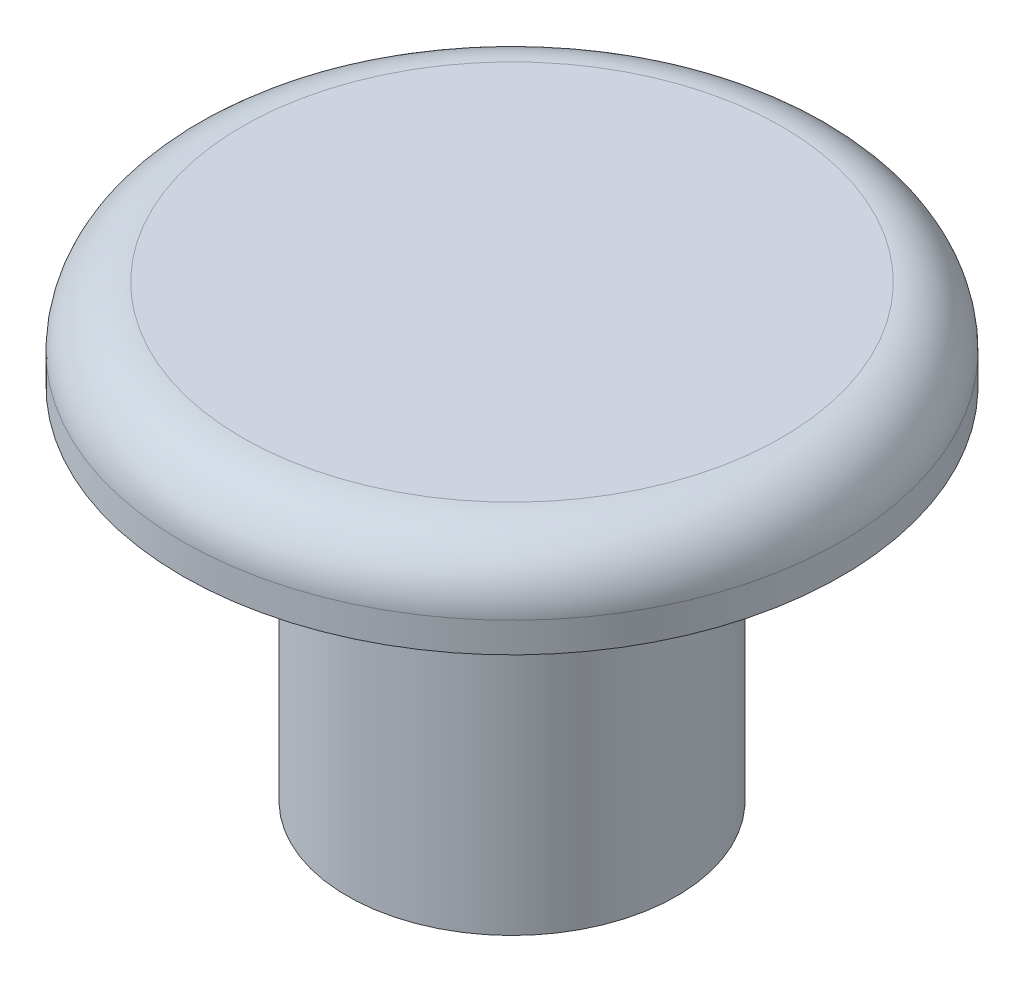
SolidWorks part; units mm, degrees
ref_plane "Front Plane" through (0, 0, 0) normal (0, 0, 1) x (1, 0, 0)
ref_plane "Top Plane" through (0, 0, 0) normal (0, 1, 0) x (1, 0, 0)
ref_plane "Right Plane" through (0, 0, 0) normal (1, 0, 0) x (0, 0, -1)
sketch "Sketch1" plane through (0, 0, 0) normal (0, 0, 1) x (1, 0, 0)
  line L0 (0, 0) -> (0, 22.4422) construction
  line L1 (0, 0) -> (5.5, 0)
  line L2 (5.5, 0) -> (5.5, 12)
  line L3 (5.5, 12) -> (11, 12)
  line L4 (11, 12) -> (11, 15)
  line L5 (11, 15) -> (0, 15)
  line L6 (0, 0) -> (0, 15)
  dimension "D1" = 12
  dimension "D2" = 3
  dimension "D3" = 5.5
  dimension "D4" = 11
revolve "Revolve1" add sketch "Sketch1" angle 360 about L0
fillet "Fillet1" radius 2 1 edges at (0, 15, -11)
